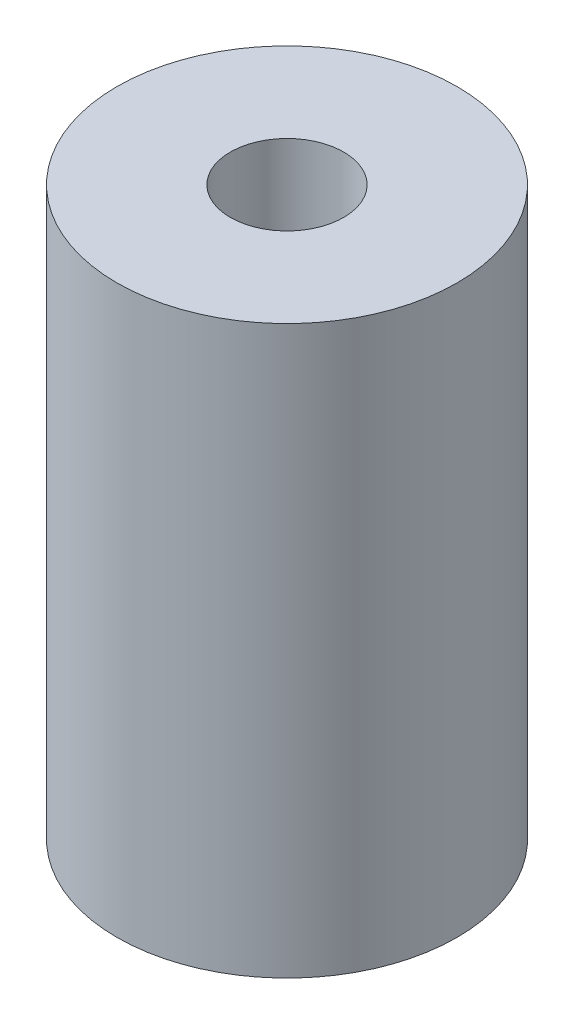
SolidWorks part; units mm, degrees
ref_plane "Front Plane" through (0, 0, 0) normal (0, 0, 1) x (1, 0, 0)
ref_plane "Top Plane" through (0, 0, 0) normal (0, 1, 0) x (1, 0, 0)
ref_plane "Right Plane" through (0, 0, 0) normal (1, 0, 0) x (0, 0, -1)
sketch "Sketch1" plane through (0, 0, 0) normal (0, 1, 0) x (1, 0, 0)
  circle A0 centre (0, 0) radius 15
  circle A4 centre (0, 0) radius 5
extrude "Boss-Extrude1" add sketch "Sketch1" along normal blind 50
sketch "wrap" plane through (0, 0, 0) normal (0, 0, 1) x (1, 0, 0)
  line L0 (0, 35) -> (0, 30)
  line L1 (48.53, 30) -> (48.53, 35)
  spline S0 degree 3 poles (0, 30) (25.778, 17.9795) (20.08, 43.2664) (48.53, 30) knots 0 0 0 0 1 1 1 1
  spline S1 degree 3 poles (0, 35) (25.778, 22.9795) (20.08, 48.2664) (48.53, 35) knots 0 0 0 0 1 1 1 1
